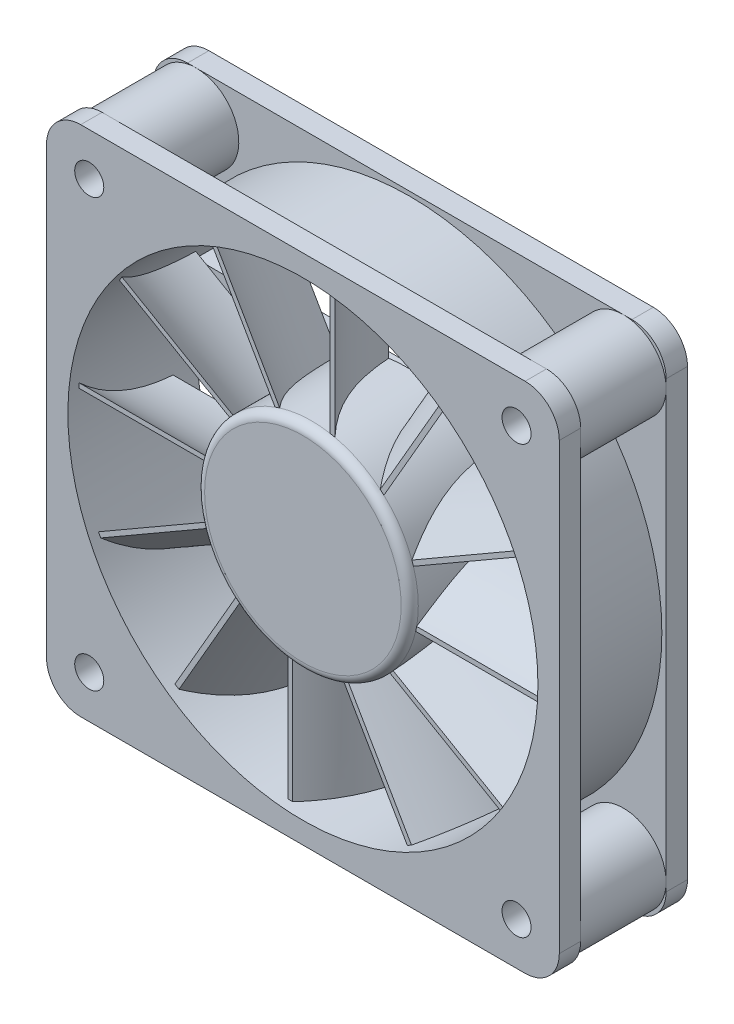
SolidWorks part; units mm, degrees
material "ABS"
ref_plane "Front Plane" through (0, 0, 0) normal (0, 0, 1) x (1, 0, 0)
ref_plane "Top Plane" through (0, 0, 0) normal (0, 1, 0) x (1, 0, 0)
ref_plane "Right Plane" through (0, 0, 0) normal (1, 0, 0) x (0, 0, -1)
sketch "Sketch1" plane through (0, 0, 0) normal (0, 0, 1) x (1, 0, 0)
  line L1 (-27.6482, 24.7228) -> (32.3518, 24.7228)
  line L2 (-27.6482, 24.7228) -> (-27.6482, -35.2772)
  line L3 (-27.6482, -35.2772) -> (32.3518, -35.2772)
  line L4 (32.3518, 24.7228) -> (32.3518, -35.2772)
  circle A0 centre (2.3518, -5.2772) radius 27.5
  circle A1 centre (-22.6482, 19.7228) radius 1.7
  circle A2 centre (27.3518, 19.7228) radius 1.7
  circle A3 centre (27.3518, -30.2772) radius 1.7
  circle A4 centre (-22.6482, -30.2772) radius 1.7
  dimension "D5" = 55
  dimension "D8" = 3.4
  dimension "D1" = 60
  dimension "D2" = 60
  dimension "D3" = 30
  dimension "D4" = 30
  dimension "D6" = 5
  dimension "D7" = 5
  dimension "D11" = 50
  dimension "D12" = 50
  dimension "D9" = 2
  dimension "D10" = 2
extrude "Boss-Extrude1" add sketch "Sketch1" along normal blind 15
ref_plane "Plane1" through (0, 0, 7.5) normal (0, 0, 1) x (1, 0, 0)
sketch "Sketch2" plane through (0, 0, 7.5) normal (0, 0, 1) x (1, 0, 0)
  line L0 (-27.6482, -35.2772) -> (32.3518, -35.2772) construction
  line L1 (32.3518, -35.2772) -> (32.3518, 24.7228) construction
  line L2 (-27.6482, 24.7228) -> (-27.6482, -35.2772) construction
  line L3 (32.3518, 24.7228) -> (-27.6482, 24.7228) construction
  line L4 (-27.6482, -35.2772) -> (32.3518, -35.2772)
  line L5 (32.3518, -35.2772) -> (32.3518, 24.7228)
  line L6 (-27.6482, 24.7228) -> (-27.6482, -35.2772)
  line L7 (32.3518, 24.7228) -> (-27.6482, 24.7228)
  circle A0 centre (2.3518, -5.2772) radius 29.5
  circle A1 centre (2.3518, -5.2772) radius 27.5 construction
  dimension "D1" = 2
extrude "Cut-Extrude1" cut sketch "Sketch2" against normal blind 5 and the other way blind 5
fillet "Fillet1" radius 4 8 edges at (32.3518, -35.2772, 13.75) (32.3518, -35.2772, 1.25) (32.3518, 24.7228, 13.75) (32.3518, 24.7228, 1.25) (-27.6482, -35.2772, 1.25) (-27.6482, -35.2772, 13.75) (-27.6482, 24.7228, 1.25) (-27.6482, 24.7228, 13.75)
sketch "Sketch3" plane through (0, 0, 12.5) normal (0, 0, -1) x (-1, 0, 0)
  line L0 (-28.3518, 24.7228) -> (23.6482, 24.7228) construction
  line L1 (-32.3518, -31.2772) -> (-32.3518, 20.7228) construction
  circle A1 centre (-27.3518, 19.7228) radius 5
  circle A2 centre (-27.3518, 19.7228) radius 4
  dimension "D1" = 1
  dimension "D2" = 10
  dimension "D3" = 5
  dimension "D4" = 5
extrude "Boss-Extrude3" add sketch "Sketch3" along normal blind 10
ref_plane "Plane2" through (2.3518, 0, 0) normal (1, 0, 0) x (0, 0, -1)
ref_plane "Plane3" through (0, -5.2772, 0) normal (0, 1, 0) x (1, 0, 0)
mirror "Mirror1" about plane through (2.3518, 0, 0) normal (1, 0, 0) of "Boss-Extrude3"
mirror "Mirror2" about plane through (0, -5.2772, 0) normal (0, 1, 0) of "Mirror1", "Boss-Extrude3"
sketch "Sketch4" plane through (0, 0, 0) normal (0, 0, -1) x (-1, 0, 0)
  line L0 (-2.3518, 4.7228) -> (23.1927, 4.9073)
  line L1 (24.4205, 1.0072) -> (5.4267, 1.0072)
  line L2 (-2.3518, 1.375) -> (-2.3518, -1.375) construction
  line L3 (-29.8518, -5.2772) -> (25.1482, -5.2772) construction
  line L4 (1.375, -5.2772) -> (-1.375, -5.2772) construction
  line L5 (-2.3518, -32.7772) -> (-2.3518, 22.2228) construction
  line L8 (-2.3518, -15.2772) -> (-27.8964, -15.4618)
  line L9 (-29.1315, -11.5301) -> (-10.1303, -11.5617)
  line L10 (-8.6046, 21.5025) -> (-8.6363, 2.5013)
  line L11 (-12.3518, -5.2772) -> (-12.5364, 20.2673)
  line L12 (3.9327, -32.0495) -> (3.9327, -13.0558)
  line L13 (7.6482, -5.2772) -> (7.8328, -30.8218)
  circle A1 centre (-2.3518, -5.2772) radius 27.5 construction
  arc A2 (-2.3518, 4.7228) -> (5.4267, 1.0072) centre (-2.3518, -5.2772) cw
  arc A3 (23.1927, 4.9073) -> (24.4205, 1.0072) centre (-2.3518, -5.2772) cw
  arc A6 (-27.8964, -15.4618) -> (-29.1315, -11.5301) centre (-2.3518, -5.2772) cw
  arc A7 (-10.1303, -11.5617) -> (-2.3518, -15.2772) centre (-2.3518, -5.2772) ccw
  arc A8 (-8.6363, 2.5013) -> (-12.3518, -5.2772) centre (-2.3518, -5.2772) ccw
  arc A9 (-12.5364, 20.2673) -> (-8.6046, 21.5025) centre (-2.3518, -5.2772) cw
  arc A10 (7.6482, -5.2772) -> (3.9327, -13.0558) centre (-2.3518, -5.2772) cw
  arc A11 (7.8328, -30.8218) -> (3.9327, -32.0495) centre (-2.3518, -5.2772) cw
  circle A12 centre (-2.3518, -5.2772) radius 10
  point P29 (-2.3518, -5.2772)
  point P31 (-2.3518, -5.2772)
  dimension "D1" = 2
  dimension "D2" = 10
  dimension "D4" = 2
extrude "Boss-Extrude4" add sketch "Sketch4" against normal blind 2
sketch "Sketch5" plane through (0, 0, 2) normal (0, 0, 1) x (1, 0, 0)
  circle A0 centre (2.3518, -5.2772) radius 12.5
  dimension "D1" = 25
extrude "Boss-Extrude5" add sketch "Sketch5" along normal blind 12 from offset 1 separate body
fillet "Fillet2" radius 1 1 edges at (14.8518, -5.2772, 15)
sketch "Sketch6" plane through (0, -5.2772, 0) normal (0, 1, 0) x (1, 0, 0)
  line L3 (14.8518, -14) -> (-10.1482, -14) construction
  line L9 (14.8518, -3) -> (-10.1482, -3) construction
  line L11 (-0.1504, -3) -> (0.3866, -3)
  line L13 (4.5413, -14) -> (5.1, -14)
  spline S0 degree 2 poles (0.3866, -3) (0.8548, -9.4289) (5.1, -14) knots 0 0 0 1 1 1
  spline S1 degree 2 poles (-0.1504, -3) (0.3216, -9.4179) (4.5413, -14) knots 0 0 0 1 1 1
extrude "Boss-Extrude6" add sketch "Sketch6" along normal blind 17.2 from offset 10
sketch "Sketch7" plane through (0, 0, 15) normal (0, 0, 1) x (1, 0, 0)
  line L0 (-0.1504, 21.9228) -> (-0.1504, 6.9697) construction
  line L1 (5.1, 21.9228) -> (5.1, 6.9169) construction
  line L2 (-0.1504, 22.0068) -> (-0.1504, 21.7609)
  line L3 (5.1, 21.9831) -> (5.1, 21.737)
  arc A0 (-0.1504, 21.7609) -> (5.1, 21.737) centre (2.3518, -5.2772) cw
  arc A1 (-0.1504, 22.0068) -> (5.1, 21.9831) centre (2.3518, -5.2772) cw
extrude "Cut-Extrude2" cut sketch "Sketch7" against normal blind 12
sketch "Sketch8" plane through (2.3518, 0, 0) normal (1, 0, 0) x (0, 0, -1)
  line L0 (0, -5.2772) -> (-15.9705, -5.2772) construction
  line L1 (0, -31.2772) -> (0, 20.7228) construction
  line L2 (1.375, -5.2772) -> (-1.375, -5.2772) construction
pattern_circular "CirPattern1" count 12 over 360 about axis through (2.3518, -5.2772, 0) along (0, 0, 1) of "Boss-Extrude6"
